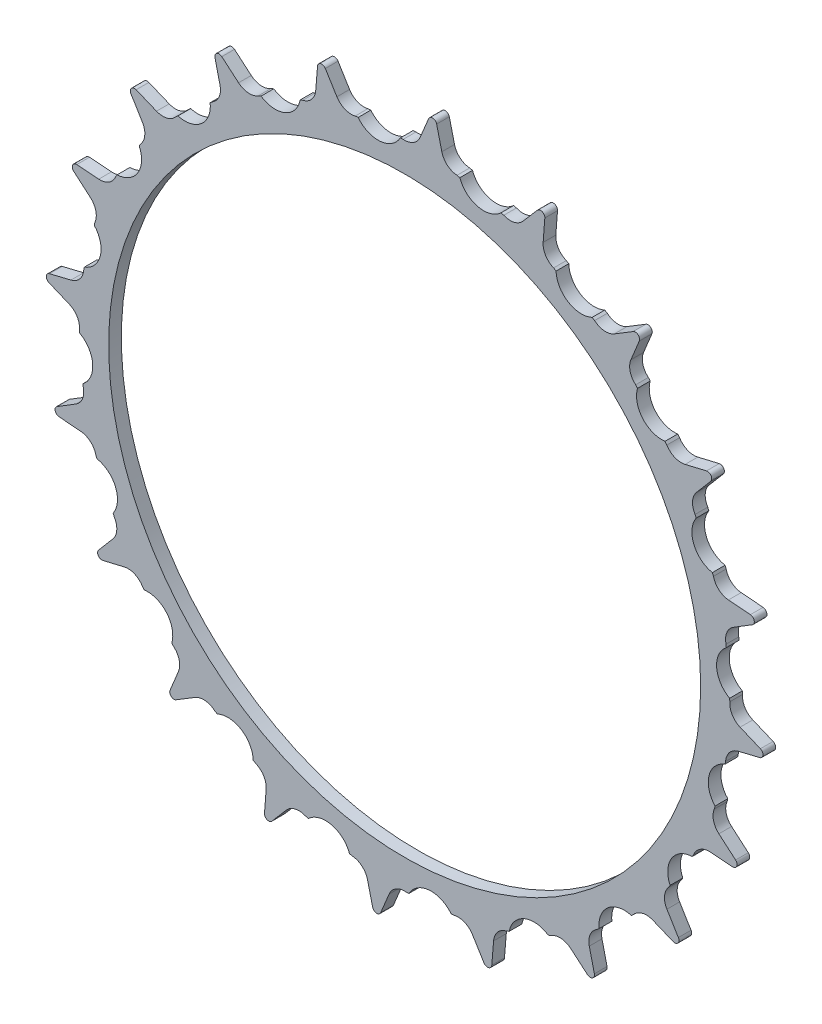
SolidWorks part; units mm, degrees
ref_plane "Front Plane" through (0, 0, 0) normal (0, 0, 1) x (1, 0, 0)
ref_plane "Top Plane" through (0, 0, 0) normal (0, 1, 0) x (1, 0, 0)
ref_plane "Right Plane" through (0, 0, 0) normal (1, 0, 0) x (0, 0, -1)
sketch "Sketch1" plane through (0, 0, 0) normal (0, 0, 1) x (1, 0, 0)
  line L0 (3.6626, 79.3215) -> (5.6677, 84.1262)
  line L1 (3.6626, 79.3215) -> (8.7911, 78.9179) construction
  line L2 (7.5623, 83.9771) -> (8.7911, 78.9179)
  line L3 (3.6626, 79.3215) -> (0, 0) construction
  line L4 (0, 0) -> (8.7911, 78.9179) construction
  line L5 (16.0261, 77.772) -> (18.7582, 82.2038)
  line L6 (20.6061, 81.7602) -> (21.0283, 76.5711)
  line L7 (27.995, 74.3074) -> (31.3867, 78.2573)
  line L8 (33.1425, 77.5301) -> (32.7478, 72.3388)
  line L9 (39.2746, 69.0132) -> (43.2424, 72.3839)
  line L10 (44.8629, 71.3909) -> (43.6609, 66.3253)
  line L11 (49.5871, 62.0196) -> (54.0334, 64.7281)
  line L12 (55.4785, 63.4939) -> (53.4989, 58.6786)
  line L13 (58.6786, 53.4989) -> (63.4939, 55.4785)
  line L14 (64.7281, 54.0334) -> (62.0196, 49.5871)
  line L15 (66.3253, 43.6609) -> (71.3909, 44.8629)
  line L16 (72.3839, 43.2424) -> (69.0132, 39.2746)
  line L17 (72.3388, 32.7478) -> (77.5301, 33.1425)
  line L18 (78.2573, 31.3867) -> (74.3074, 27.995)
  line L19 (76.5711, 21.0283) -> (81.7602, 20.6061)
  line L20 (82.2038, 18.7582) -> (77.772, 16.0261)
  line L21 (78.9179, 8.7911) -> (83.9771, 7.5623)
  line L22 (84.1262, 5.6677) -> (79.3215, 3.6626)
  line L23 (79.3215, -3.6626) -> (84.1262, -5.6677)
  line L24 (83.9771, -7.5623) -> (78.9179, -8.7911)
  line L25 (77.772, -16.0261) -> (82.2038, -18.7582)
  line L26 (81.7602, -20.6061) -> (76.5711, -21.0283)
  line L27 (74.3074, -27.995) -> (78.2573, -31.3867)
  line L28 (77.5301, -33.1425) -> (72.3388, -32.7478)
  line L29 (69.0132, -39.2746) -> (72.3839, -43.2424)
  line L30 (71.3909, -44.8629) -> (66.3253, -43.6609)
  line L31 (62.0196, -49.5871) -> (64.7281, -54.0334)
  line L32 (63.4939, -55.4785) -> (58.6786, -53.4989)
  line L33 (53.4989, -58.6786) -> (55.4785, -63.4939)
  line L34 (54.0334, -64.7281) -> (49.5871, -62.0196)
  line L35 (43.6609, -66.3253) -> (44.8629, -71.3909)
  line L36 (43.2424, -72.3839) -> (39.2746, -69.0132)
  line L37 (32.7478, -72.3388) -> (33.1425, -77.5301)
  line L38 (31.3867, -78.2573) -> (27.995, -74.3074)
  line L39 (21.0283, -76.5711) -> (20.6061, -81.7602)
  line L40 (18.7582, -82.2038) -> (16.0261, -77.772)
  line L41 (8.7911, -78.9179) -> (7.5623, -83.9771)
  line L42 (5.6677, -84.1262) -> (3.6626, -79.3215)
  line L43 (-3.6626, -79.3215) -> (-5.6677, -84.1262)
  line L44 (-7.5623, -83.9771) -> (-8.7911, -78.9179)
  line L45 (-16.0261, -77.772) -> (-18.7582, -82.2038)
  line L46 (-20.6061, -81.7602) -> (-21.0283, -76.5711)
  line L47 (-27.995, -74.3074) -> (-31.3867, -78.2573)
  line L48 (-33.1425, -77.5301) -> (-32.7478, -72.3388)
  line L49 (-39.2746, -69.0132) -> (-43.2424, -72.3839)
  line L50 (-44.8629, -71.3909) -> (-43.6609, -66.3253)
  line L51 (-49.5871, -62.0196) -> (-54.0334, -64.7281)
  line L52 (-55.4785, -63.4939) -> (-53.4989, -58.6786)
  line L53 (-58.6786, -53.4989) -> (-63.4939, -55.4785)
  line L54 (-64.7281, -54.0334) -> (-62.0196, -49.5871)
  line L55 (-66.3253, -43.6609) -> (-71.3909, -44.8629)
  line L56 (-72.3839, -43.2424) -> (-69.0132, -39.2746)
  line L57 (-72.3388, -32.7478) -> (-77.5301, -33.1425)
  line L58 (-78.2573, -31.3867) -> (-74.3074, -27.995)
  line L59 (-76.5711, -21.0283) -> (-81.7602, -20.6061)
  line L60 (-82.2038, -18.7582) -> (-77.772, -16.0261)
  line L61 (-78.9179, -8.7911) -> (-83.9771, -7.5623)
  line L62 (-84.1262, -5.6677) -> (-79.3215, -3.6626)
  line L63 (-79.3215, 3.6626) -> (-84.1262, 5.6677)
  line L64 (-83.9771, 7.5623) -> (-78.9179, 8.7911)
  line L65 (-77.772, 16.0261) -> (-82.2038, 18.7582)
  line L66 (-81.7602, 20.6061) -> (-76.5711, 21.0283)
  line L67 (-74.3074, 27.995) -> (-78.2573, 31.3867)
  line L68 (-77.5301, 33.1425) -> (-72.3388, 32.7478)
  line L69 (-69.0132, 39.2746) -> (-72.3839, 43.2424)
  line L70 (-71.3909, 44.8629) -> (-66.3253, 43.6609)
  line L71 (-62.0196, 49.5871) -> (-64.7281, 54.0334)
  line L72 (-63.4939, 55.4785) -> (-58.6786, 53.4989)
  line L73 (-53.4989, 58.6786) -> (-55.4785, 63.4939)
  line L74 (-54.0334, 64.7281) -> (-49.5871, 62.0196)
  line L75 (-43.6609, 66.3253) -> (-44.8629, 71.3909)
  line L76 (-43.2424, 72.3839) -> (-39.2746, 69.0132)
  line L77 (-32.7478, 72.3388) -> (-33.1425, 77.5301)
  line L78 (-31.3867, 78.2573) -> (-27.995, 74.3074)
  line L79 (-21.0283, 76.5711) -> (-20.6061, 81.7602)
  line L80 (-18.7582, 82.2038) -> (-16.0261, 77.772)
  line L81 (-8.7911, 78.9179) -> (-7.5623, 83.9771)
  line L82 (-5.6677, 84.1262) -> (-3.6626, 79.3215)
  line L83 (0, 80.85) -> (0, 0) construction
  line L84 (0, 0) -> (6.5906, 83.7411) construction
  circle A0 centre (0, 0) radius 80.85 construction
  arc A1 (-3.9676, 80.7526) -> (3.6626, 79.3215) centre (0, 80.85) ccw
  arc A2 (4.2537, 80.738) -> (8.4288, 80.4094) centre (0, 0) cw
  arc A3 (5.6677, 84.1262) -> (7.5623, 83.9771) centre (6.5906, 83.7411) cw
  arc A4 (8.7138, 80.3791) -> (16.0261, 77.772) centre (12.6477, 79.8546) ccw
  arc A5 (18.7582, 82.2038) -> (20.6061, 81.7602) centre (19.6094, 81.6791) cw
  arc A6 (21.1806, 78.0263) -> (27.995, 74.3074) centre (24.984, 76.8929) ccw
  arc A7 (31.3867, 78.2573) -> (33.1425, 77.5301) centre (32.1454, 77.6059) cw
  arc A8 (33.1258, 73.7523) -> (39.2746, 69.0132) centre (36.7051, 72.0379) ccw
  arc A9 (43.2424, 72.3839) -> (44.8629, 71.3909) centre (43.8899, 71.6218) cw
  arc A10 (44.2554, 67.6623) -> (49.5871, 62.0196) centre (47.5224, 65.409) ccw
  arc A11 (54.0334, 64.7281) -> (55.4785, 63.4939) centre (54.5536, 63.8741) cw
  arc A12 (54.2952, 59.9062) -> (58.6786, 53.4989) centre (57.1696, 57.1696) ccw
  arc A13 (63.4939, 55.4785) -> (64.7281, 54.0334) centre (63.8741, 54.5536) cw
  arc A14 (62.9981, 50.675) -> (66.3253, 43.6609) centre (65.409, 47.5224) ccw
  arc A15 (71.3909, 44.8629) -> (72.3839, 43.2424) centre (71.6218, 43.8899) cw
  arc A16 (70.1499, 40.196) -> (72.3388, 32.7478) centre (72.0379, 36.7051) ccw
  arc A17 (77.5301, 33.1425) -> (78.2573, 31.3867) centre (77.6059, 32.1454) cw
  arc A18 (75.5742, 28.7273) -> (76.5711, 21.0283) centre (76.8929, 24.984) ccw
  arc A19 (81.7602, 20.6061) -> (82.2038, 18.7582) centre (81.6791, 19.6094) cw
  arc A20 (79.1377, 16.5512) -> (78.9179, 8.7911) centre (79.8546, 12.6477) ccw
  arc A21 (83.9771, 7.5623) -> (84.1262, 5.6677) centre (83.7411, 6.5906) cw
  arc A22 (80.7526, 3.9676) -> (79.3215, -3.6626) centre (80.85, 0) ccw
  arc A23 (84.1262, -5.6677) -> (83.9771, -7.5623) centre (83.7411, -6.5906) cw
  arc A24 (80.3791, -8.7138) -> (77.772, -16.0261) centre (79.8546, -12.6477) ccw
  arc A25 (82.2038, -18.7582) -> (81.7602, -20.6061) centre (81.6791, -19.6094) cw
  arc A26 (78.0263, -21.1806) -> (74.3074, -27.995) centre (76.8929, -24.984) ccw
  arc A27 (78.2573, -31.3867) -> (77.5301, -33.1425) centre (77.6059, -32.1454) cw
  arc A28 (73.7523, -33.1258) -> (69.0132, -39.2746) centre (72.0379, -36.7051) ccw
  arc A29 (72.3839, -43.2424) -> (71.3909, -44.8629) centre (71.6218, -43.8899) cw
  arc A30 (67.6623, -44.2554) -> (62.0196, -49.5871) centre (65.409, -47.5224) ccw
  arc A31 (64.7281, -54.0334) -> (63.4939, -55.4785) centre (63.8741, -54.5536) cw
  arc A32 (59.9062, -54.2952) -> (53.4989, -58.6786) centre (57.1696, -57.1696) ccw
  arc A33 (55.4785, -63.4939) -> (54.0334, -64.7281) centre (54.5536, -63.8741) cw
  arc A34 (50.675, -62.9981) -> (43.6609, -66.3253) centre (47.5224, -65.409) ccw
  arc A35 (44.8629, -71.3909) -> (43.2424, -72.3839) centre (43.8899, -71.6218) cw
  arc A36 (40.196, -70.1499) -> (32.7478, -72.3388) centre (36.7051, -72.0379) ccw
  arc A37 (33.1425, -77.5301) -> (31.3867, -78.2573) centre (32.1454, -77.6059) cw
  arc A38 (28.7273, -75.5742) -> (21.0283, -76.5711) centre (24.984, -76.8929) ccw
  arc A39 (20.6061, -81.7602) -> (18.7582, -82.2038) centre (19.6094, -81.6791) cw
  arc A40 (16.5512, -79.1377) -> (8.7911, -78.9179) centre (12.6477, -79.8546) ccw
  arc A41 (7.5623, -83.9771) -> (5.6677, -84.1262) centre (6.5906, -83.7411) cw
  arc A42 (3.9676, -80.7526) -> (-3.6626, -79.3215) centre (0, -80.85) ccw
  arc A43 (-5.6677, -84.1262) -> (-7.5623, -83.9771) centre (-6.5906, -83.7411) cw
  arc A44 (-8.7138, -80.3791) -> (-16.0261, -77.772) centre (-12.6477, -79.8546) ccw
  arc A45 (-18.7582, -82.2038) -> (-20.6061, -81.7602) centre (-19.6094, -81.6791) cw
  arc A46 (-21.1806, -78.0263) -> (-27.995, -74.3074) centre (-24.984, -76.8929) ccw
  arc A47 (-31.3867, -78.2573) -> (-33.1425, -77.5301) centre (-32.1454, -77.6059) cw
  arc A48 (-33.1258, -73.7523) -> (-39.2746, -69.0132) centre (-36.7051, -72.0379) ccw
  arc A49 (-43.2424, -72.3839) -> (-44.8629, -71.3909) centre (-43.8899, -71.6218) cw
  arc A50 (-44.2554, -67.6623) -> (-49.5871, -62.0196) centre (-47.5224, -65.409) ccw
  arc A51 (-54.0334, -64.7281) -> (-55.4785, -63.4939) centre (-54.5536, -63.8741) cw
  arc A52 (-54.2952, -59.9062) -> (-58.6786, -53.4989) centre (-57.1696, -57.1696) ccw
  arc A53 (-63.4939, -55.4785) -> (-64.7281, -54.0334) centre (-63.8741, -54.5536) cw
  arc A54 (-62.9981, -50.675) -> (-66.3253, -43.6609) centre (-65.409, -47.5224) ccw
  arc A55 (-71.3909, -44.8629) -> (-72.3839, -43.2424) centre (-71.6218, -43.8899) cw
  arc A56 (-70.1499, -40.196) -> (-72.3388, -32.7478) centre (-72.0379, -36.7051) ccw
  arc A57 (-77.5301, -33.1425) -> (-78.2573, -31.3867) centre (-77.6059, -32.1454) cw
  arc A58 (-75.5742, -28.7273) -> (-76.5711, -21.0283) centre (-76.8929, -24.984) ccw
  arc A59 (-81.7602, -20.6061) -> (-82.2038, -18.7582) centre (-81.6791, -19.6094) cw
  arc A60 (-79.1377, -16.5512) -> (-78.9179, -8.7911) centre (-79.8546, -12.6477) ccw
  arc A61 (-83.9771, -7.5623) -> (-84.1262, -5.6677) centre (-83.7411, -6.5906) cw
  arc A62 (-80.7526, -3.9676) -> (-79.3215, 3.6626) centre (-80.85, 0) ccw
  arc A63 (-84.1262, 5.6677) -> (-83.9771, 7.5623) centre (-83.7411, 6.5906) cw
  arc A64 (-80.3791, 8.7138) -> (-77.772, 16.0261) centre (-79.8546, 12.6477) ccw
  arc A65 (-82.2038, 18.7582) -> (-81.7602, 20.6061) centre (-81.6791, 19.6094) cw
  arc A66 (-78.0263, 21.1806) -> (-74.3074, 27.995) centre (-76.8929, 24.984) ccw
  arc A67 (-78.2573, 31.3867) -> (-77.5301, 33.1425) centre (-77.6059, 32.1454) cw
  arc A68 (-73.7523, 33.1258) -> (-69.0132, 39.2746) centre (-72.0379, 36.7051) ccw
  arc A69 (-72.3839, 43.2424) -> (-71.3909, 44.8629) centre (-71.6218, 43.8899) cw
  arc A70 (-67.6623, 44.2554) -> (-62.0196, 49.5871) centre (-65.409, 47.5224) ccw
  arc A71 (-64.7281, 54.0334) -> (-63.4939, 55.4785) centre (-63.8741, 54.5536) cw
  arc A72 (-59.9062, 54.2952) -> (-53.4989, 58.6786) centre (-57.1696, 57.1696) ccw
  arc A73 (-55.4785, 63.4939) -> (-54.0334, 64.7281) centre (-54.5536, 63.8741) cw
  arc A74 (-50.675, 62.9981) -> (-43.6609, 66.3253) centre (-47.5224, 65.409) ccw
  arc A75 (-44.8629, 71.3909) -> (-43.2424, 72.3839) centre (-43.8899, 71.6218) cw
  arc A76 (-40.196, 70.1499) -> (-32.7478, 72.3388) centre (-36.7051, 72.0379) ccw
  arc A77 (-33.1425, 77.5301) -> (-31.3867, 78.2573) centre (-32.1454, 77.6059) cw
  arc A78 (-28.7273, 75.5742) -> (-21.0283, 76.5711) centre (-24.984, 76.8929) ccw
  arc A79 (-20.6061, 81.7602) -> (-18.7582, 82.2038) centre (-19.6094, 81.6791) cw
  arc A80 (-16.5512, 79.1377) -> (-8.7911, 78.9179) centre (-12.6477, 79.8546) ccw
  arc A81 (-7.5623, 83.9771) -> (-5.6677, 84.1262) centre (-6.5906, 83.7411) cw
  point P289 (0, 0)
  dimension "D1" = 161.7
  dimension "D2" = 3.9688
  dimension "D5" = 1
  dimension "D6" = 84
  dimension "D3" = 4.5
  dimension "D4" = 40
extrude "Boss-Extrude1" add sketch "Sketch1" along normal blind 3 contours A81 L81 A80 L80 A79 L79 A78 L78 A77 L77 A76 L76 A75 L75 A74 L74 A73 L73 A72 L72 A71 L71 A70 L70 A69 L69 A68 L68 A67 L67 A66 L66 A65 L65 A64 L64 A63 L63 A62 L62 A61 L61 A60 L60 A59 L59 A58 L58 A57 L57 A56 | A3 L0 A2 L2
sketch "Sketch2" plane through (0, 0, 3) normal (0, 0, 1) x (1, 0, 0)
  circle A0 centre (0, 0) radius 12.5
  dimension "D1" = 25
extrude "Boss-Extrude2" add sketch "Sketch2" along normal blind 40
fillet "Fillet1" radius 30 1 edges at (12.5, 0, 3)
sketch "Sketch3" plane through (0, 0, 43) normal (0, 0, 1) x (1, 0, 0)
  circle A0 centre (0, 0) radius 5
  dimension "D1" = 10
extrude "Cut-Extrude1" cut sketch "Sketch3" against normal through all
hole_wizard "Ø1.0mm Dowel Hole1" positions "3DSketch1" profile "Sketch4" hole size "Ø1.0" standard "ANSI Metric"
sketch3d "3DSketch1"
  point P0 (-6.8176, -10.4771, 42.0201)
  point P2 (-11.0684, 5.8086, 41.6583)
sketch "Sketch4" plane through (-6.8176, -10.4771, 42.0201) normal (0, 0, 1) x (0.8382, -0.5454, 0)
  line L0 (0, 0) -> (0, 34)
  line L1 (0, 34) -> (1.4, 33.1588)
  line L2 (1.4, 33.1588) -> (1.4, 0)
  line L5 (1.4, 0) -> (0, 0)
  line L10 (0, 34) -> (-1.4, 33.1588) construction
  line L11 (0, -6.35) -> (0, 107.95) construction
  dimension "Hole Dia." = 2.8
  dimension "Hole Depth" = 34
  dimension "Drill Angle" = 118
sketch "Sketch5" plane through (0, 0, 0) normal (0, 0, -1) x (-1, 0, 0)
  line L0 (-0.9617, 76.9995) -> (1.0322, 76.8426)
  line L1 (-0.9617, 76.9995) -> (-0.3094, 85.2872)
  line L2 (12.9952, 75.9011) -> (13.6474, 84.1888)
  line L3 (-0.3094, 85.2872) -> (13.6474, 84.1888)
  line L4 (11.0014, 76.058) -> (12.9952, 75.9011)
  arc A0 (1.0322, 76.8426) -> (11.0014, 76.058) centre (6.277, 79.7567) ccw
  arc A2 (7.5623, 83.9771) -> (5.6677, 84.1262) centre (6.5906, 83.7411) ccw construction
  arc A3 (-3.6626, 79.3215) -> (3.6626, 79.3215) centre (0, 80.85) ccw construction
  arc A4 (8.7911, 78.9179) -> (16.0261, 77.772) centre (12.6477, 79.8546) ccw construction
  point P17 (6.669, 84.738)
  dimension "D2" = 2
  dimension "D3" = 2
  dimension "D4" = 6
  dimension "D1" = 14
extrude "Cut-Extrude2" cut sketch "Sketch5" against normal blind 10
pattern_circular "CirPattern1" count 20 over 360 about axis through (0, 0, 0) along (0, 0, 1) of "Cut-Extrude2"
sketch "Sketch7" plane through (0, 0, 0) normal (0, 0, -1) x (-1, 0, 0)
  line L1 (12.5, -7.2169) -> (12.5, 7.2169)
  line L2 (12.5, 7.2169) -> (0, 14.4338)
  line L3 (0, 14.4338) -> (-12.5, 7.2169)
  line L4 (-12.5, 7.2169) -> (-12.5, -7.2169)
  line L5 (-12.5, -7.2169) -> (0, -14.4338)
  line L6 (0, -14.4338) -> (12.5, -7.2169)
  circle A0 centre (0, 0) radius 12.5 construction
  point P1 (0, 0)
  dimension "D1" = 25
extrude "Cut-Extrude3" cut sketch "Sketch7" against normal through all
sketch "Sketch8" plane through (0, 0, 0) normal (0, 1, 0) x (1, 0, 0)
  line L1 (-83.9771, -3) -> (90.5942, -3)
  line L2 (-83.9771, -3) -> (-83.9771, -42.7162)
  line L3 (-83.9771, -42.7162) -> (90.5942, -42.7162)
  line L4 (90.5942, -3) -> (90.5942, -42.7162)
extrude "Cut-Extrude4" cut sketch "Sketch8" against normal through all both and the other way through all
sketch "Sketch9" plane through (0, 0, 3) normal (0, 0, 1) x (1, 0, 0)
  circle A0 centre (0, 0) radius 70
  dimension "D1" = 140
extrude "Cut-Extrude5" cut sketch "Sketch9" against normal through all
sketch "Sketch10" plane through (0, 0, 3) normal (0, 0, 1) x (1, 0, 0)
  line L0 (-46.7524, 102.6837) -> (-46.7524, 25.1593)
  line L1 (-46.6524, 102.5837) -> (98.7175, 102.5837)
  line L2 (-46.6524, 102.5837) -> (-46.6524, 25.2593)
  line L3 (-46.6524, 25.2593) -> (98.7175, 25.2593)
  line L4 (98.7175, 102.5837) -> (98.7175, 25.2593)
  line L5 (-46.7524, 25.1593) -> (98.8175, 25.1593)
  line L6 (98.8175, 102.6837) -> (98.8175, 25.1593)
  line L7 (-46.7524, 102.6837) -> (98.8175, 102.6837)
  dimension "D1" = 0.1
extrude "Cut-Extrude6" [suppressed] cut sketch "Sketch10" against normal through all
